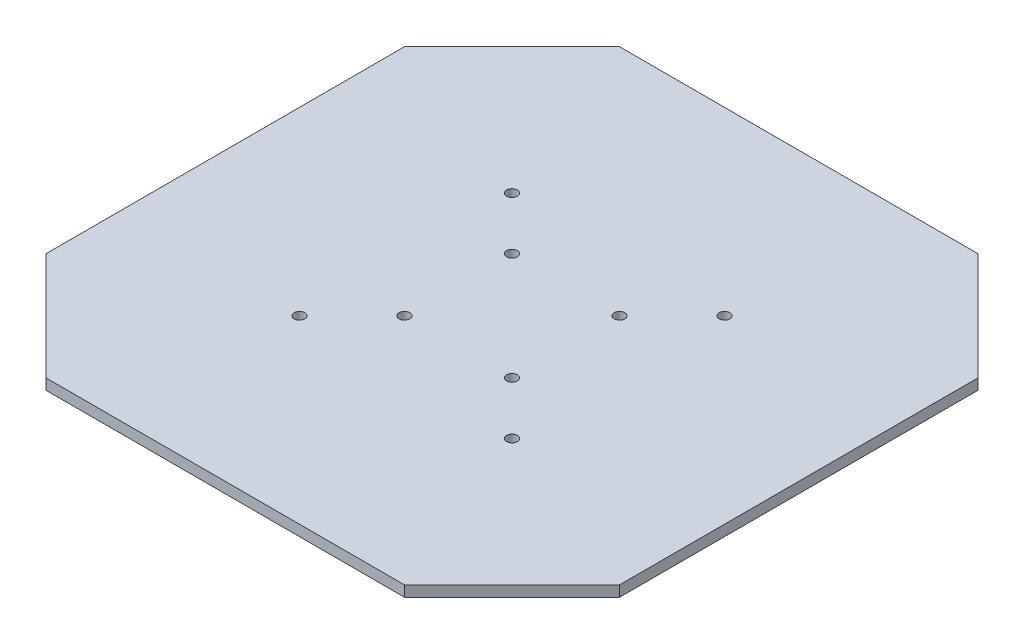
SolidWorks part; units mm, degrees
ref_plane "Front Plane" through (0, 0, 0) normal (0, 0, 1) x (1, 0, 0)
ref_plane "Top Plane" through (0, 0, 0) normal (0, 1, 0) x (1, 0, 0)
ref_plane "Right Plane" through (0, 0, 0) normal (1, 0, 0) x (0, 0, -1)
sketch "Sketch1" plane through (0, 0, 0) normal (0, 1, 0) x (1, 0, 0)
  line L0 (0, 130) -> (30, 160)
  line L1 (30, 0) -> (130, 0)
  line L2 (0, 30) -> (0, 130)
  line L3 (30, 160) -> (130, 160)
  line L4 (160, 30) -> (160, 130)
  line L5 (130, 160) -> (160, 130)
  line L6 (30, 0) -> (0, 30)
  line L7 (130, 0) -> (160, 30)
  point P0 (0, 0)
  point P1 (160, 160)
  point P2 (0, 160)
  point P3 (160, 0)
extrude "Boss-Extrude1" add sketch "Sketch1" along normal blind 3
sketch "Sketch3" plane through (0, 0, 0) normal (0, -1, 0) x (1, 0, 0)
  line L0 (0, -80) -> (160, -80)
  line L1 (0, -130) -> (0, -30) construction
  line L2 (160, -30) -> (160, -130) construction
  line L3 (80, -160) -> (80, 0)
  line L4 (130, -160) -> (30, -160) construction
  line L5 (30, 0) -> (130, 0) construction
  line L6 (15, -145) -> (145, -15)
  line L7 (30, -160) -> (0, -130) construction
  line L8 (130, 0) -> (160, -30) construction
  line L9 (15, -15) -> (145, -145)
  line L10 (0, -30) -> (30, 0) construction
  line L11 (160, -130) -> (130, -160) construction
  circle A0 centre (109.6447, -50.3553) radius 1.5
  circle A1 centre (50.3553, -109.6447) radius 1.5
  circle A2 centre (50.3553, -50.3553) radius 1.5
  circle A3 centre (109.6447, -109.6447) radius 1.5
  circle A4 centre (65, -95) radius 1.5
  circle A5 centre (95, -95) radius 1.5
  circle A6 centre (65, -65) radius 1.5
  circle A7 centre (95, -65) radius 1.5
  point P40 (0, 0)
  point P41 (0, 0)
  point P42 (0, 0)
  point P43 (0, 0)
  dimension "D1" = 50
  dimension "D2" = 50
  dimension "D5" = 30
  dimension "D3" = 50
  dimension "D4" = 50
extrude "Cut-Extrude1" cut sketch "Sketch3" against normal blind 10 contours L9 A2 | L9 A2 | L6 A0 | L6 A0 | L9 A3 | L9 A3 | L6 A1 | L6 A1 | A4 | A5 | A6 | A7
